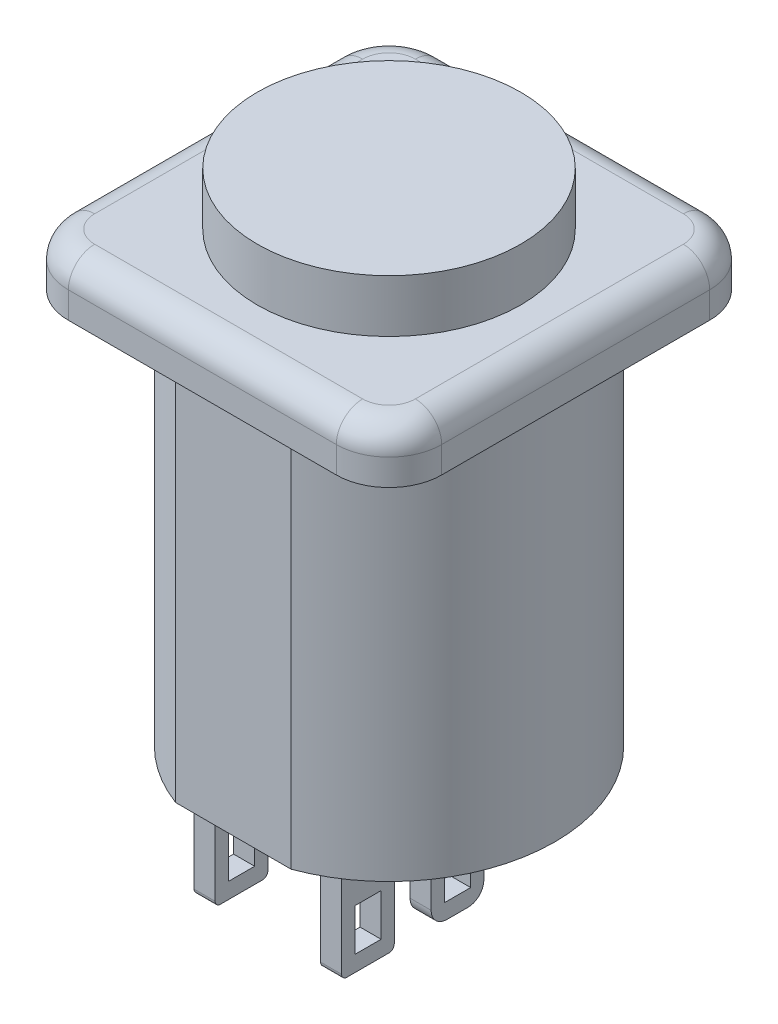
SolidWorks part; units mm, degrees
ref_plane "Front Plane" through (0, 0, 0) normal (0, 0, 1) x (1, 0, 0)
ref_plane "Top Plane" through (0, 0, 0) normal (0, 1, 0) x (1, 0, 0)
ref_plane "Right Plane" through (0, 0, 0) normal (1, 0, 0) x (0, 0, -1)
sketch "Sketch1" plane through (0, 0, 0) normal (0, 1, 0) x (1, 0, 0)
  line L0 (0, 0) -> (0, 7.5) construction
  line L1 (-2.7839, 7.5) -> (2.7839, 7.5)
  line L2 (1.163, 0) -> (-1.163, 0) construction
  line L3 (-2.7839, -7.5) -> (2.7839, -7.5)
  arc A0 (-2.7839, 7.5) -> (-2.7839, -7.5) centre (0, 0) ccw
  arc A1 (2.7839, -7.5) -> (2.7839, 7.5) centre (0, 0) ccw
  point P7 (0, 7.5)
  point P9 (0, 0)
  dimension "D1" = 16
  dimension "D2" = 15
extrude "Boss-Extrude1" add sketch "Sketch1" along normal blind 19.05 contours A0 L3 A1 L1
sketch "Sketch2" plane through (0, 19.05, 0) normal (0, 1, 0) x (1, 0, 0)
  line L1 (9, -9) -> (-9, -9)
  line L2 (9, -9) -> (9, 9)
  line L3 (9, 9) -> (-9, 9)
  line L4 (-9, -9) -> (-9, 9)
  line L5 (9, -9) -> (-9, 9) construction
  line L6 (9, 9) -> (-9, -9) construction
  point P0 (0, 0)
  dimension "D1" = 18
  dimension "D2" = 18
extrude "Boss-Extrude2" add sketch "Sketch2" along normal blind 2.54
fillet "Fillet1" radius 2.54 4 edges at (9, 20.32, -9) (-9, 20.32, -9) (-9, 20.32, 9) (9, 20.32, 9)
fillet "Fillet2" radius 1.27 8 edges at (-8.2561, 21.59, 8.2561) (-9, 21.59, 0) (-8.2561, 21.59, -8.2561) (0, 21.59, -9) (8.2561, 21.59, -8.2561) (9, 21.59, 0) (8.2561, 21.59, 8.2561) (0, 21.59, 9)
sketch "Sketch3" plane through (0, 21.59, 0) normal (0, 1, 0) x (1, 0, 0)
  circle A0 centre (0, 0) radius 6.35
  dimension "D1" = 12.7
extrude "Boss-Extrude3" add sketch "Sketch3" along normal blind 2.54 separate body
sketch "Sketch4" plane through (0, 0, 0) normal (0, -1, 0) x (1, 0, 0)
  line L0 (0, 0) -> (0, 7.5) construction
  line L1 (-2.7839, 7.5) -> (2.7839, 7.5) construction
  line L2 (3.556, -1.016) -> (2.54, -1.016)
  line L3 (-3.556, 5.842) -> (-2.54, 5.842)
  line L4 (-3.556, 5.842) -> (-3.556, 3.302)
  line L5 (-3.556, 3.302) -> (-2.54, 3.302)
  line L6 (-2.54, 5.842) -> (-2.54, 3.302)
  line L7 (-3.556, 1.524) -> (-2.54, 1.524)
  line L8 (-3.556, 1.524) -> (-3.556, -1.016)
  line L9 (-3.556, -1.016) -> (-2.54, -1.016)
  line L10 (-2.54, 1.524) -> (-2.54, -1.016)
  line L11 (2.54, 1.524) -> (2.54, -1.016)
  line L12 (3.556, 1.524) -> (2.54, 1.524)
  line L13 (3.556, 1.524) -> (3.556, -1.016)
  line L14 (3.556, 3.302) -> (2.54, 3.302)
  line L15 (2.54, 5.842) -> (2.54, 3.302)
  line L16 (3.556, 5.842) -> (2.54, 5.842)
  line L17 (3.556, 5.842) -> (3.556, 3.302)
  dimension "D1" = 1.016
  dimension "D2" = 2.54
  dimension "D3" = 1.016
  dimension "D4" = 2.54
  dimension "D5" = 1.778
  dimension "D6" = 1.524
  dimension "D7" = 2.54
extrude "Boss-Extrude5" add sketch "Sketch4" along normal blind 5.08 separate body
sketch "Sketch5" plane through (-3.556, 0, 0) normal (-1, 0, 0) x (0, 0, 1)
  line L0 (4.572, -5.08) -> (4.572, 0) construction
  line L1 (5.842, -5.08) -> (3.302, -5.08) construction
  line L2 (5.842, 0) -> (3.302, 0) construction
  line L3 (0.254, -5.08) -> (0.254, 0) construction
  line L4 (3.937, -4.318) -> (5.207, -4.318)
  line L5 (3.937, -4.318) -> (3.937, -2.286)
  line L6 (3.937, -2.286) -> (5.207, -2.286)
  line L7 (5.207, -4.318) -> (5.207, -2.286)
  line L8 (3.937, -4.318) -> (5.207, -2.286) construction
  line L9 (3.937, -2.286) -> (5.207, -4.318) construction
  line L10 (1.524, -5.08) -> (-1.016, -5.08) construction
  line L11 (1.524, 0) -> (-1.016, 0) construction
  line L13 (-0.381, -2.286) -> (0.889, -2.286)
  line L14 (-0.381, -2.286) -> (-0.381, -4.318)
  line L15 (-0.381, -4.318) -> (0.889, -4.318)
  line L16 (0.889, -2.286) -> (0.889, -4.318)
  line L17 (-0.381, -2.286) -> (0.889, -4.318) construction
  line L18 (-0.381, -4.318) -> (0.889, -2.286) construction
  point P6 (4.572, -3.302)
  point P17 (0.254, -3.302)
  dimension "D1" = 2.032
  dimension "D2" = 1.27
  dimension "D3" = 0.762
  dimension "D4" = 1.27
extrude "Cut-Extrude1" cut sketch "Sketch5" against normal blind 8.128
fillet "Fillet3" radius 0.254 2 edges at (-3.048, -5.08, 3.302) (-3.048, -5.08, 5.842)
fillet "Fillet4" radius 0.254 2 edges at (3.048, -5.08, 3.302) (3.048, -5.08, 5.842)
fillet "Fillet5" radius 0.762 2 edges at (-3.048, -5.08, -1.016) (-3.048, -5.08, 1.524)
fillet "Fillet6" radius 0.762 2 edges at (3.048, -5.08, -1.016) (3.048, -5.08, 1.524)
